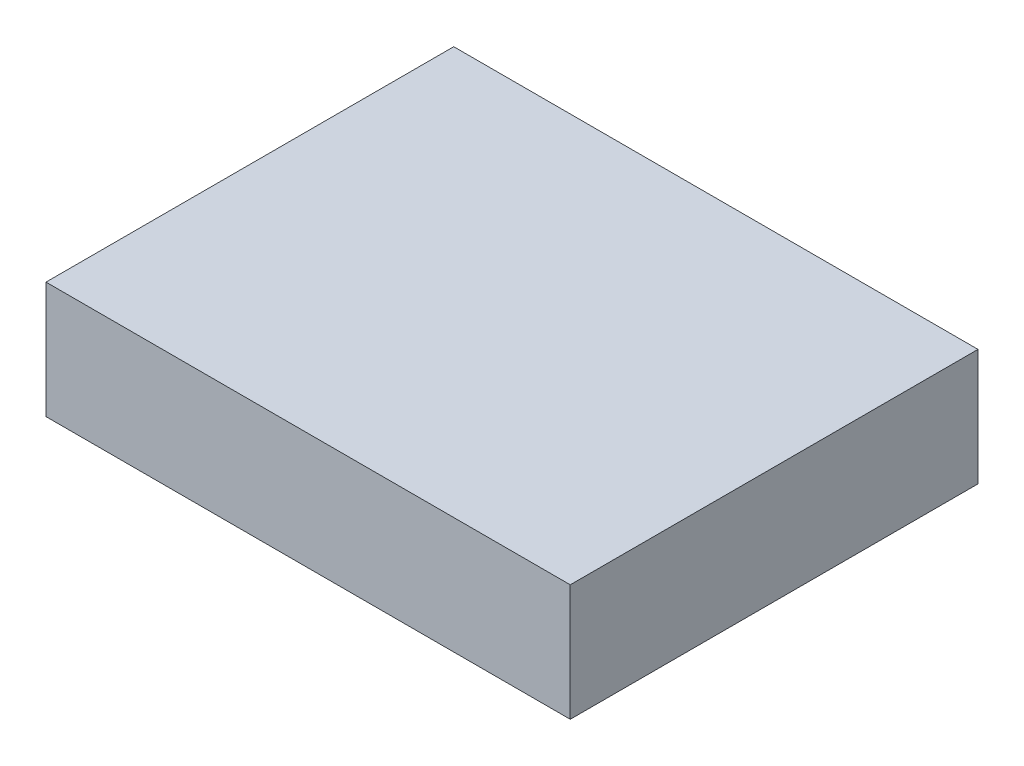
SolidWorks part; units mm, degrees
ref_plane "Front Plane" through (0, 0, 0) normal (0, 0, 1) x (1, 0, 0)
ref_plane "Top Plane" through (0, 0, 0) normal (0, 1, 0) x (1, 0, 0)
ref_plane "Right Plane" through (0, 0, 0) normal (1, 0, 0) x (0, 0, -1)
sketch "Sketch1" plane through (0, 0, 0) normal (0, 1, 0) x (1, 0, 0)
  line L1 (-22.86, -17.78) -> (22.86, -17.78)
  line L2 (-22.86, -17.78) -> (-22.86, 17.78)
  line L3 (-22.86, 17.78) -> (22.86, 17.78)
  line L4 (22.86, -17.78) -> (22.86, 17.78)
  line L5 (-22.86, -17.78) -> (22.86, 17.78) construction
  line L6 (-22.86, 17.78) -> (22.86, -17.78) construction
  point P0 (0, 0)
  dimension "D1" = 45.72
  dimension "D2" = 35.56
extrude "Boss-Extrude1" add sketch "Sketch1" along normal blind 10.16
